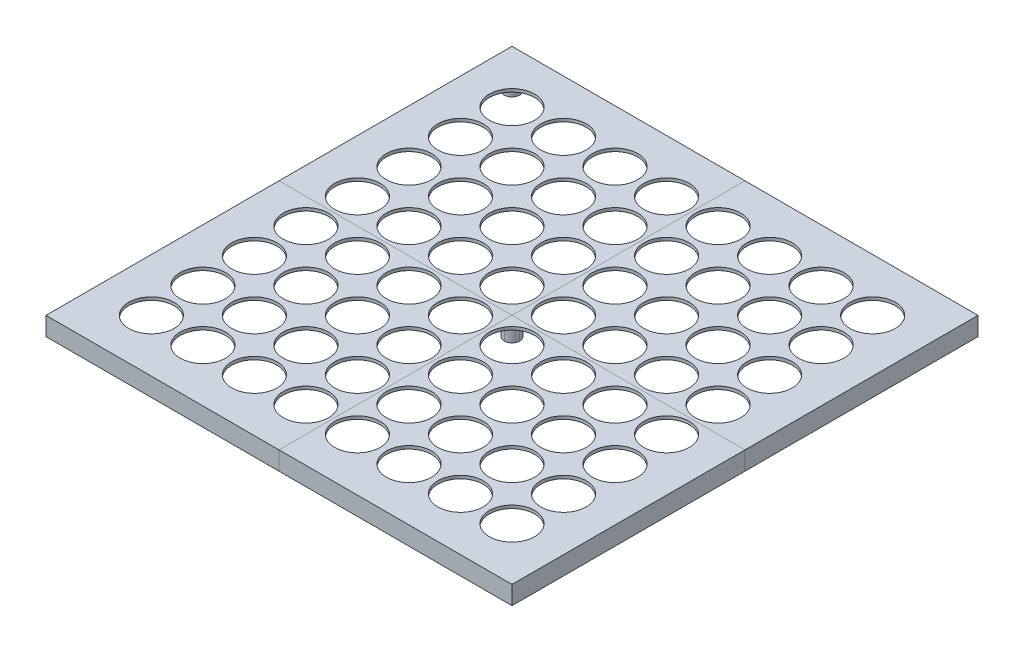
SolidWorks part; units mm, degrees
ref_plane "Front Plane" through (0, 0, 0) normal (0, 0, 1) x (1, 0, 0)
ref_plane "Top Plane" through (0, 0, 0) normal (0, 1, 0) x (1, 0, 0)
ref_plane "Right Plane" through (0, 0, 0) normal (1, 0, 0) x (0, 0, -1)
sketch "Sketch5" plane through (0, 0, 0) normal (0, 1, 0) x (1, 0, 0)
  line L1 (0, 0) -> (303, 0)
  line L2 (0, 0) -> (0, 303)
  line L3 (0, 303) -> (303, 303)
  line L4 (303, 0) -> (303, 303)
  dimension "D1" = 303
  dimension "D2" = 303
extrude "Boss-Extrude4" add sketch "Sketch5" along normal blind 2
sketch "Sketch7" plane through (0, 2, 0) normal (0, 1, 0) x (1, 0, 0)
  circle A0 centre (34.25, 34.25) radius 14.75
extrude "Cut-Extrude5" cut sketch "Sketch7" against normal through all contours A0
pattern_linear "LPattern7" count 8 spacing 33.5 along (0, 0, -1) count 8 spacing 33.5 along (1, 0, 0) of "Cut-Extrude5"
sketch "Sketch13" plane through (0, 0, 0) normal (0, 1, 0) x (1, 0, 0)
  line L1 (0, 303) -> (303, 303)
  line L2 (0, 303) -> (0, 0)
  line L3 (0, 0) -> (303, 0)
  line L4 (303, 303) -> (303, 0)
sketch "Sketch14" plane through (0, 0, 0) normal (0, 1, 0) x (1, 0, 0)
  line L1 (0, 303) -> (303, 303)
  line L2 (0, 303) -> (0, 0)
  line L3 (0, 0) -> (303, 0)
  line L4 (303, 303) -> (303, 0)
extrude "Boss-Extrude7" add sketch "Sketch14" against normal blind 10
sketch "Sketch15" plane through (0, 0, 0) normal (0, 1, 0) x (1, 0, 0)
  line L1 (3, 3) -> (300, 3)
  line L2 (3, 3) -> (3, 300)
  line L3 (3, 300) -> (300, 300)
  line L4 (300, 3) -> (300, 300)
extrude "Cut-Extrude6" cut sketch "Sketch15" against normal blind 10
sketch "Sketch16" plane through (0, 0, 0) normal (0, -1, 0) x (-1, 0, 0)
  circle A0 centre (-151.5, 151.5) radius 5
extrude "Boss-Extrude8" add sketch "Sketch16" along normal blind 10
sketch "Sketch17" plane through (0, 0, 0) normal (0, 1, 0) x (1, 0, 0)
  circle A0 centre (13, 13) radius 5
extrude "Boss-Extrude10" add sketch "Sketch17" against normal blind 10
sketch "Sketch18" plane through (0, 0, 0) normal (0, 1, 0) x (1, 0, 0)
  circle A0 centre (13, 290) radius 5
  circle A1 centre (290, 290) radius 5
  circle A2 centre (290, 13) radius 5
extrude "Boss-Extrude11" add sketch "Sketch18" against normal blind 10
sketch "Sketch20" plane through (0, 0, 0) normal (0, 1, 0) x (1, 0, 0)
  line L0 (151.5, 303) -> (151.5, 0)
  line L1 (0, 303) -> (303, 303) construction
  line L2 (0, 0) -> (303, 0) construction
  line L3 (0, 151.5) -> (303, 151.5)
  line L4 (0, 303) -> (0, 0) construction
  line L5 (303, 303) -> (303, 0) construction
split "Split1" trim tools "Sketch20" bodies to split 123 resulting bodies 124 125 126 127
